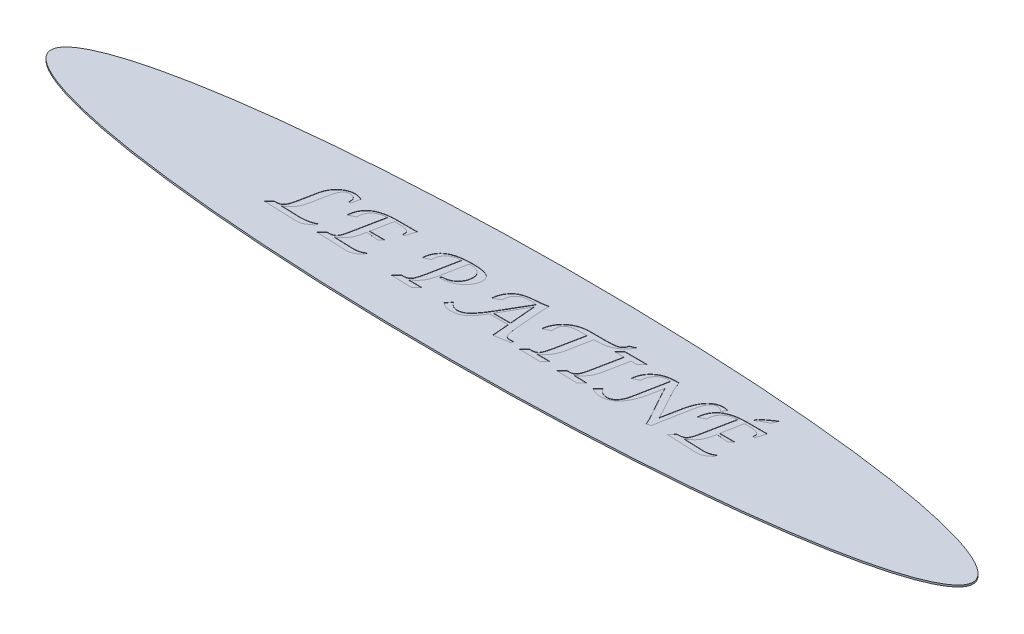
SolidWorks part; units mm, degrees
material "Silicio"
ref_plane "Alzado" through (0, 0, 0) normal (0, 0, 1) x (1, 0, 0)
ref_plane "Planta" through (0, 0, 0) normal (0, 1, 0) x (1, 0, 0)
ref_plane "Vista lateral" through (0, 0, 0) normal (1, 0, 0) x (0, 0, -1)
sketch "Croquis1" plane through (0, 0, 0) normal (0, 1, 0) x (1, 0, 0)
  ellipse E0 centre (0, 0) end of major axis (135, 0) minor radius 20
  dimension "D1" = 270
  dimension "D2" = 40
extrude "Saliente-Extruir1" add sketch "Croquis1" along normal blind 0.5
sketch "Croquis3" plane through (0, 0.5, 0) normal (0, 1, 0) x (1, 0, 0)
  line L0 (-111.8138, -7.301) -> (111.8138, -7.301) construction
  text T0 "LE PATINÉ" font "Lucida Calligraphy" height 15
  point P3 (0, -7.301)
extrude "Cortar-Extruir2" cut sketch "Croquis3" against normal blind 0.1
